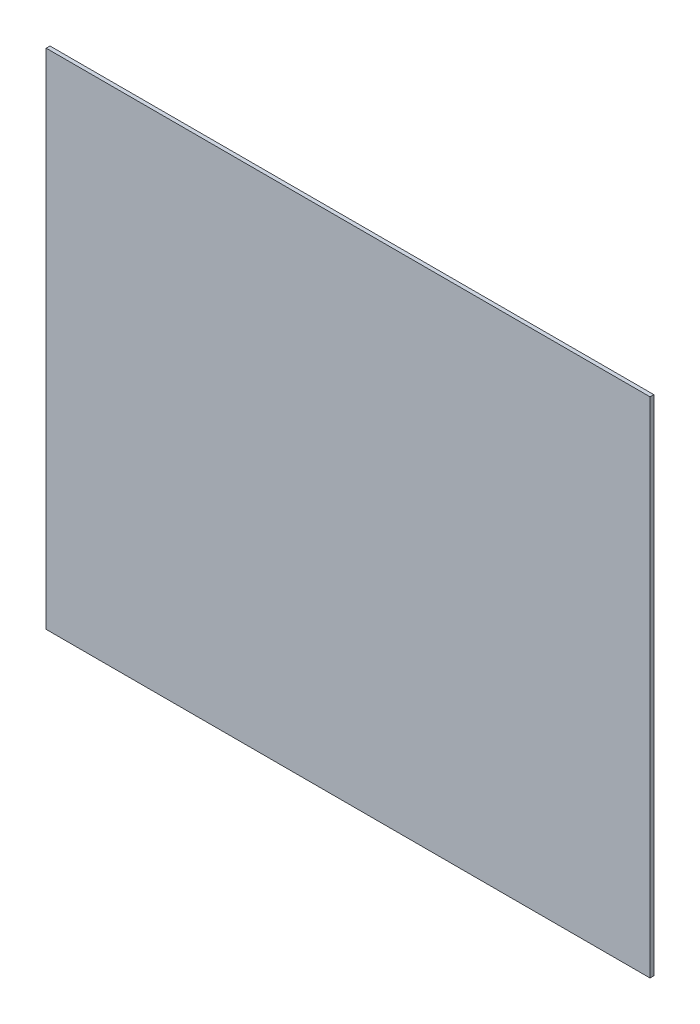
SolidWorks part; units mm, degrees
ref_plane "Front Plane" through (0, 0, 0) normal (0, 0, 1) x (1, 0, 0)
ref_plane "Top Plane" through (0, 0, 0) normal (0, 1, 0) x (1, 0, 0)
ref_plane "Right Plane" through (0, 0, 0) normal (1, 0, 0) x (0, 0, -1)
sketch "Sketch1" plane through (0, 0, 0) normal (0, 0, 1) x (1, 0, 0)
  line L1 (-237.5, -198) -> (237.5, -198)
  line L2 (-237.5, -198) -> (-237.5, 198)
  line L3 (-237.5, 198) -> (237.5, 198)
  line L4 (237.5, -198) -> (237.5, 198)
  line L5 (-237.5, -198) -> (237.5, 198) construction
  line L6 (-237.5, 198) -> (237.5, -198) construction
  point P0 (0, 0)
  dimension "D1" = 475
  dimension "D2" = 396
extrude "Boss-Extrude1" add sketch "Sketch1" along normal blind 3
